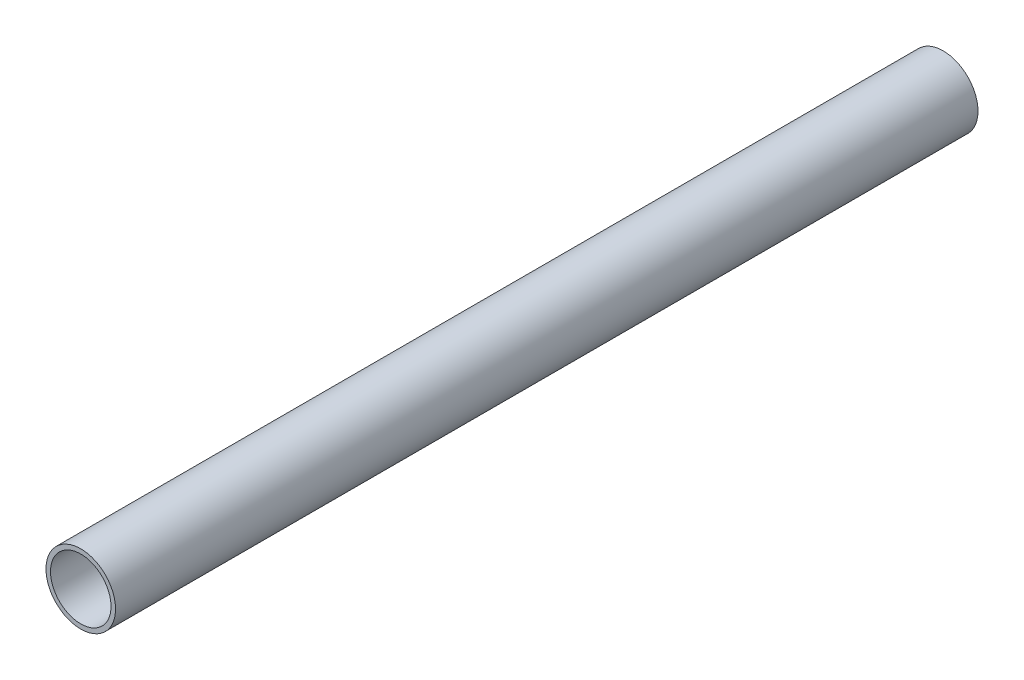
SolidWorks part; units mm, degrees
material "PVC Rigid"
ref_plane "Front Plane" through (0, 0, 0) normal (0, 0, 1) x (1, 0, 0)
ref_plane "Top Plane" through (0, 0, 0) normal (0, 1, 0) x (1, 0, 0)
ref_plane "Right Plane" through (0, 0, 0) normal (1, 0, 0) x (0, 0, -1)
sketch "Sketch1" plane through (0, 0, 0) normal (0, 0, 1) x (1, 0, 0)
  circle A0 centre (0, 0) radius 26.2509
  circle A1 centre (0, 0) radius 30.1625
  dimension "D1" = 60.325
  dimension "D2" = 3.9116
extrude "Boss-Extrude1" add sketch "Sketch1" along normal up to surface (747.9032 mm away)
